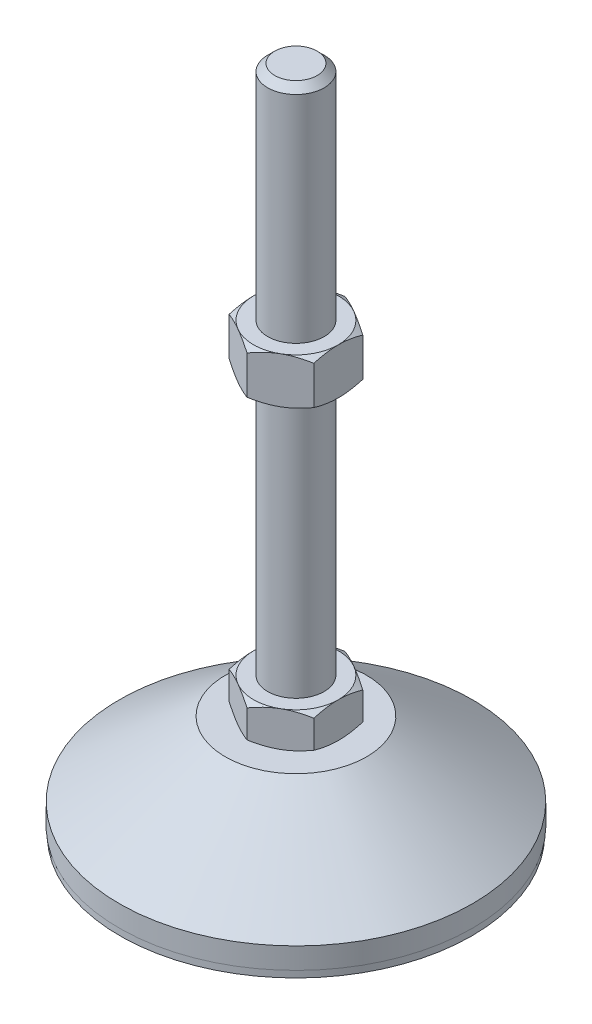
SolidWorks part; units mm, degrees
ref_plane "Спереди" through (0, 0, 0) normal (0, 0, 1) x (1, 0, 0)
ref_plane "Сверху" through (0, 0, 0) normal (0, 1, 0) x (1, 0, 0)
ref_plane "Справа" through (0, 0, 0) normal (1, 0, 0) x (0, 0, -1)
sketch "Эскиз1" plane through (0, 0, 0) normal (0, 0, 1) x (1, 0, 0)
  line L0 (0, 0) -> (-49.8, 0)
  line L1 (-49.8, 0) -> (-49.8, 2)
  line L2 (-49.8, 2) -> (-50, 2)
  line L3 (-50, 2) -> (-50, 8)
  line L4 (-50, 8) -> (-20, 29)
  line L5 (-20, 29) -> (-8, 29)
  line L12 (-8, 39) -> (-8, 187)
  line L13 (-8, 187) -> (-6, 189)
  line L14 (-6, 189) -> (0, 189)
  line L15 (0, 189) -> (0, 0) construction
  line L16 (-8, 29) -> (0, 29) construction
  line L17 (0, 0) -> (0, 189)
  line L18 (0, 0) -> (0, -7.9595) construction
  line L19 (-8, 39) -> (-8, 29)
  point P8 (-8, 113)
  point P23 (-14, 29)
  dimension "D1" = 16
  dimension "D2" = 29
  dimension "D3" = 10
  dimension "D4" = 100
  dimension "D5" = 8
  dimension "D6" = 2
  dimension "D7" = 45
  dimension "D8" = 40
  dimension "D9" = 2
  dimension "D10" = 150
  dimension "D11" = 6
  dimension "D12" = 0.2
revolve "Повернуть1" add sketch "Эскиз1" angle 360 about L17
sketch "Эскиз2" plane through (0, 29, 0) normal (0, 1, 0) x (1, 0, 0)
  line L1 (0, 13.8564) -> (-12, 6.9282)
  line L2 (-12, 6.9282) -> (-12, -6.9282)
  line L3 (-12, -6.9282) -> (0, -13.8564)
  line L4 (0, -13.8564) -> (12, -6.9282)
  line L5 (12, -6.9282) -> (12, 6.9282)
  line L6 (12, 6.9282) -> (0, 13.8564)
  circle A0 centre (0, 0) radius 12 construction
  dimension "D1" = 24
extrude "Бобышка-Вытянуть1" add sketch "Эскиз2" along normal up to vertex (10 mm away) up to point (-8, 39, 0)
ref_plane "Плоскость1" through (0, 113, 0) normal (0, 1, 0) x (1, 0, 0)
sketch "Эскиз3" plane through (0, 113, 0) normal (0, 1, 0) x (1, 0, 0)
  line L6 (12, 6.9282) -> (0, 13.8564)
  line L7 (0, 13.8564) -> (-12, 6.9282)
  line L8 (-12, 6.9282) -> (-12, -6.9282)
  line L9 (-12, -6.9282) -> (0, -13.8564)
  line L10 (0, -13.8564) -> (12, -6.9282)
  line L11 (12, -6.9282) -> (12, 6.9282)
  line L12 (12, 6.9282) -> (0, 13.8564)
  line L13 (0, 13.8564) -> (-12, 6.9282)
  line L14 (-12, 6.9282) -> (-12, -6.9282)
  line L15 (-12, -6.9282) -> (0, -13.8564)
  line L16 (0, -13.8564) -> (12, -6.9282)
  line L17 (12, -6.9282) -> (12, 6.9282)
  dimension "D1" = 0
extrude "Бобышка-Вытянуть2" add sketch "Эскиз3" along normal blind 13
sketch "Эскиз4" plane through (0, 0, 0) normal (0, 0, 1) x (1, 0, 0)
  line L0 (-12, 126) -> (-23.2583, 119.5)
  line L1 (-23.2583, 119.5) -> (-23.2583, 126)
  line L2 (-23.2583, 126) -> (-12, 126)
  line L3 (-23.2583, 119.5) -> (-12, 113)
  line L4 (50, 113) -> (-50, 113) construction
  line L5 (-12, 113) -> (-23.2583, 113)
  line L6 (-23.2583, 113) -> (-23.2583, 119.5)
  line L7 (-12, 126) -> (-12, 113) construction
  line L8 (-12, 39) -> (-20.6603, 39)
  line L9 (-20.6603, 39) -> (-20.6603, 34)
  line L10 (-20.6603, 34) -> (-12, 39)
  line L11 (-12, 29) -> (-20.6603, 34)
  line L12 (-20.6603, 34) -> (-20.6603, 29)
  line L13 (-20.6603, 29) -> (-12, 29)
  line L14 (0, 189) -> (0, 96.3793) construction
  dimension "D1" = 30
  dimension "D2" = 30
revolve "Вырез-Повернуть2" cut sketch "Эскиз4" angle 360 about L14
